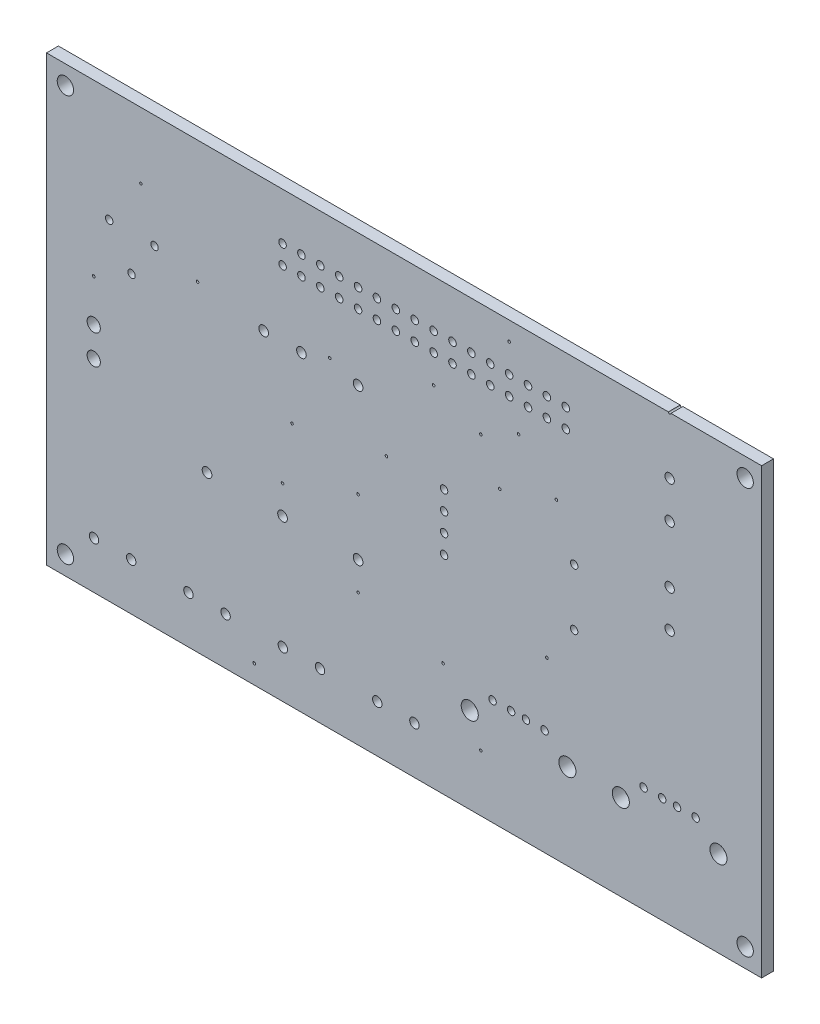
SolidWorks part; units mm, degrees
ref_plane "Front Plane" through (0, 0, 0) normal (0, 0, 1) x (1, 0, 0)
ref_plane "Top Plane" through (0, 0, 0) normal (0, 1, 0) x (1, 0, 0)
ref_plane "Right Plane" through (0, 0, 0) normal (1, 0, 0) x (0, 0, -1)
ref_plane "Dielectric_Layer Layer 1" through (0, 0, 1.6) normal (0, 0, 1) x (1, 0, 0)
sketch "Sketch1" plane through (0, 0, 0) normal (0, 0, 1) x (1, 0, 0)
  line L0 (3.81, 11.43) -> (100, 11.43)
  line L1 (100, 11.43) -> (100, 71.11)
  line L2 (100, 71.11) -> (3.81, 71.11)
  line L3 (3.81, 71.11) -> (3.81, 11.43)
extrude "Board_Outline" add sketch "Sketch1" along normal blind 1.6 separate body
sketch "Sketch2" plane through (0, 0, 0) normal (0, 0, 1) x (1, 0, 0)
  circle A0 centre (6.35, 13.97) radius 1.1
  circle A1 centre (6.35, 68.58) radius 1.1
  circle A2 centre (97.79, 68.58) radius 1.1
  circle A3 centre (97.79, 13.97) radius 1.1
  circle A4 centre (81.06, 22.9799) radius 1.15
  circle A5 centre (94.2, 22.9799) radius 1.15
  circle A6 centre (60.74, 22.9799) radius 1.15
  circle A7 centre (73.88, 22.9799) radius 1.15
  circle A8 centre (62.23, 55.88) radius 0.175
  circle A9 centre (71.12, 34.29) radius 0.175
  circle A10 centre (36.83, 44.45) radius 0.175
  circle A11 centre (41.91, 54.61) radius 0.175
  circle A12 centre (45.72, 29.21) radius 0.175
  circle A13 centre (62.23, 19.05) radius 0.175
  circle A14 centre (31.75, 13.97) radius 0.175
  circle A15 centre (55.88, 58.42) radius 0.175
  circle A16 centre (16.51, 62.23) radius 0.175
  circle A17 centre (24.13, 54.61) radius 0.175
  circle A18 centre (45.72, 40.64) radius 0.175
  circle A19 centre (49.53, 46.99) radius 0.175
  circle A20 centre (57.15, 26.67) radius 0.175
  circle A21 centre (10.16, 48.26) radius 0.175
  circle A22 centre (66.04, 68.58) radius 0.175
  circle A23 centre (87.63, 71.12) radius 0.175
  circle A24 centre (72.39, 53.34) radius 0.175
  circle A25 centre (67.31, 58.42) radius 0.175
  circle A26 centre (64.77, 50.8) radius 0.175
  circle A27 centre (35.56, 36.83) radius 0.175
extrude "NPTH" cut sketch "Sketch2" along normal through all
sketch "Sketch3" plane through (0, 0, 0) normal (0, 0, 1) x (1, 0, 0)
  circle A0 centre (18.34, 55.88) radius 0.5
  circle A1 centre (15.24, 51.08) radius 0.5
  circle A2 centre (12.24, 55.88) radius 0.5
  circle A3 centre (10.16, 38.66) radius 0.89
  circle A4 centre (10.16, 42.62) radius 0.89
  circle A5 centre (87.63, 58.46) radius 0.635
  circle A6 centre (87.63, 63.46) radius 0.635
  circle A7 centre (57.29, 46.99) radius 0.5
  circle A8 centre (57.29, 44.45) radius 0.5
  circle A9 centre (57.29, 41.91) radius 0.5
  circle A10 centre (57.29, 39.37) radius 0.5
  circle A11 centre (74.79, 39.37) radius 0.5
  circle A12 centre (74.79, 46.99) radius 0.5
  circle A13 centre (87.63, 45.76) radius 0.635
  circle A14 centre (87.63, 50.76) radius 0.635
  circle A15 centre (35.56, 64.77) radius 0.51
  circle A16 centre (35.56, 62.23) radius 0.51
  circle A17 centre (38.1, 64.77) radius 0.51
  circle A18 centre (38.1, 62.23) radius 0.51
  circle A19 centre (40.64, 64.77) radius 0.51
  circle A20 centre (40.64, 62.23) radius 0.51
  circle A21 centre (43.18, 64.77) radius 0.51
  circle A22 centre (43.18, 62.23) radius 0.51
  circle A23 centre (45.72, 64.77) radius 0.51
  circle A24 centre (45.72, 62.23) radius 0.51
  circle A25 centre (48.26, 64.77) radius 0.51
  circle A26 centre (48.26, 62.23) radius 0.51
  circle A27 centre (50.8, 64.77) radius 0.51
  circle A28 centre (50.8, 62.23) radius 0.51
  circle A29 centre (53.34, 64.77) radius 0.51
  circle A30 centre (53.34, 62.23) radius 0.51
  circle A31 centre (55.88, 64.77) radius 0.51
  circle A32 centre (55.88, 62.23) radius 0.51
  circle A33 centre (58.42, 64.77) radius 0.51
  circle A34 centre (58.42, 62.23) radius 0.51
  circle A35 centre (60.96, 64.77) radius 0.51
  circle A36 centre (60.96, 62.23) radius 0.51
  circle A37 centre (63.5, 64.77) radius 0.51
  circle A38 centre (63.5, 62.23) radius 0.51
  circle A39 centre (66.04, 64.77) radius 0.51
  circle A40 centre (66.04, 62.23) radius 0.51
  circle A41 centre (68.58, 64.77) radius 0.51
  circle A42 centre (68.58, 62.23) radius 0.51
  circle A43 centre (71.12, 64.77) radius 0.51
  circle A44 centre (71.12, 62.23) radius 0.51
  circle A45 centre (73.66, 64.77) radius 0.51
  circle A46 centre (73.66, 62.23) radius 0.51
  circle A47 centre (40.6, 17.78) radius 0.635
  circle A48 centre (35.6, 17.78) radius 0.635
  circle A49 centre (15.2, 17.78) radius 0.635
  circle A50 centre (10.2, 17.78) radius 0.635
  circle A51 centre (27.9, 17.78) radius 0.635
  circle A52 centre (22.9, 17.78) radius 0.635
  circle A53 centre (53.3, 17.78) radius 0.635
  circle A54 centre (48.3, 17.78) radius 0.635
  circle A55 centre (33.02, 53.34) radius 0.65
  circle A56 centre (25.4, 33.02) radius 0.65
  circle A57 centre (38.1, 53.34) radius 0.65
  circle A58 centre (45.72, 33.02) radius 0.65
  circle A59 centre (45.72, 53.34) radius 0.65
  circle A60 centre (35.56, 33.02) radius 0.65
  circle A61 centre (84.13, 25.69) radius 0.5
  circle A62 centre (86.63, 25.69) radius 0.5
  circle A63 centre (88.63, 25.69) radius 0.5
  circle A64 centre (91.13, 25.69) radius 0.5
  circle A65 centre (63.81, 25.69) radius 0.5
  circle A66 centre (66.31, 25.69) radius 0.5
  circle A67 centre (68.31, 25.69) radius 0.5
  circle A68 centre (70.81, 25.69) radius 0.5
extrude "PTH" cut sketch "Sketch3" along normal through all
